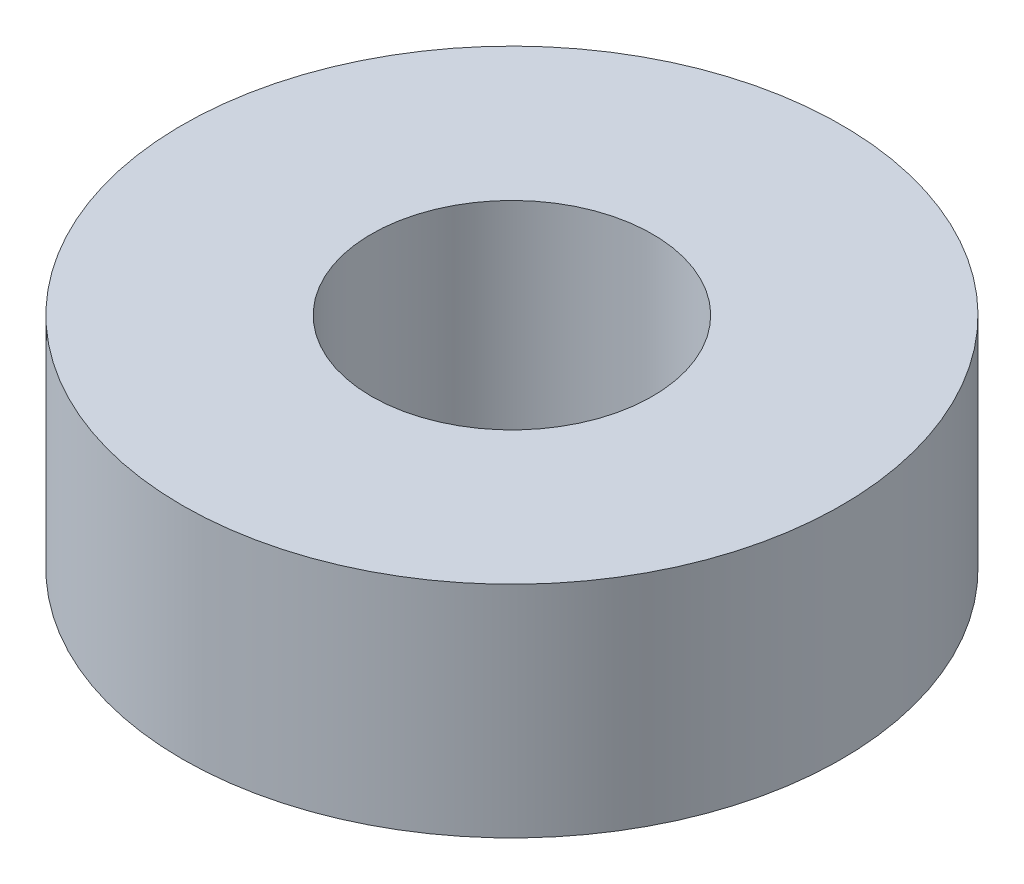
SolidWorks part; units mm, degrees
ref_plane "Front Plane" through (0, 0, 0) normal (0, 0, 1) x (1, 0, 0)
ref_plane "Top Plane" through (0, 0, 0) normal (0, 1, 0) x (1, 0, 0)
ref_plane "Right Plane" through (0, 0, 0) normal (1, 0, 0) x (0, 0, -1)
sketch "Sketch1" plane through (0, 0, 0) normal (0, 1, 0) x (1, 0, 0)
  circle A0 centre (0, 0) radius 15.24
  circle A1 centre (0, 0) radius 6.5
  dimension "D1" = 30.48
  dimension "D2" = 13
extrude "Boss-Extrude1" add sketch "Sketch1" along normal blind 10.16 contours A0 A1
